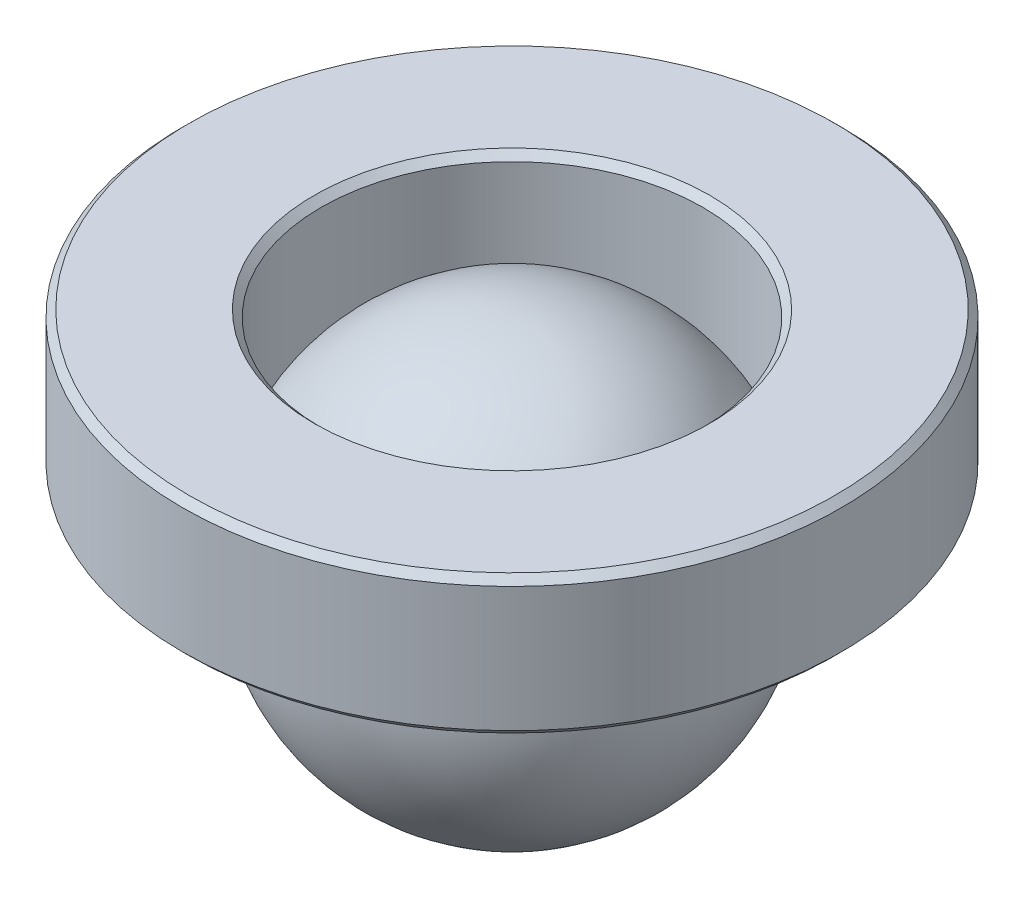
SolidWorks part; units mm, degrees
ref_plane "Alzado" through (0, 0, 0) normal (0, 0, 1) x (1, 0, 0)
ref_plane "Planta" through (0, 0, 0) normal (0, 1, 0) x (1, 0, 0)
ref_plane "Vista lateral" through (0, 0, 0) normal (1, 0, 0) x (0, 0, -1)
sketch "Croquis1" plane through (0, 0, 0) normal (0, 0, 1) x (1, 0, 0)
  line L0 (0, 3) -> (0, -3) construction
  line L1 (-2.85, 1.099) -> (-2.75, 1.199)
  line L2 (-4.65, 3.099) -> (-2.85, 3.099)
  line L3 (-4.75, 2.999) -> (-4.75, 1.199)
  line L4 (-4.65, 1.099) -> (-2.85, 1.099)
  line L5 (-2.75, 2.999) -> (-2.75, 1.199)
  line L6 (-2.85, 3.099) -> (-2.75, 2.999)
  line L7 (-4.75, 2.999) -> (-4.65, 3.099)
  line L8 (-4.75, 1.199) -> (-4.65, 1.099)
  point P4 (-4.75, 3.099)
  point P5 (-2.75, 1.099)
  point P6 (-4.75, 1.099)
  point P7 (-2.75, 3.099)
  dimension "D1" = 2.75
  dimension "D2" = 2
  dimension "D3" = 2
  dimension "D4" = 1.099
revolve "Revolución1" add sketch "Croquis1" angle 360 about L0
sketch "Croquis2" plane through (0, 0, 0) normal (0, 0, 1) x (1, 0, 0)
  line L0 (0, 3) -> (0, -3) construction
  line L1 (0, 3) -> (0, -3)
  arc A0 (0, 3) -> (0, -3) centre (0, 0) ccw
  dimension "D1" = 3
revolve "Revolución2" add sketch "Croquis2" angle 360 about L0
